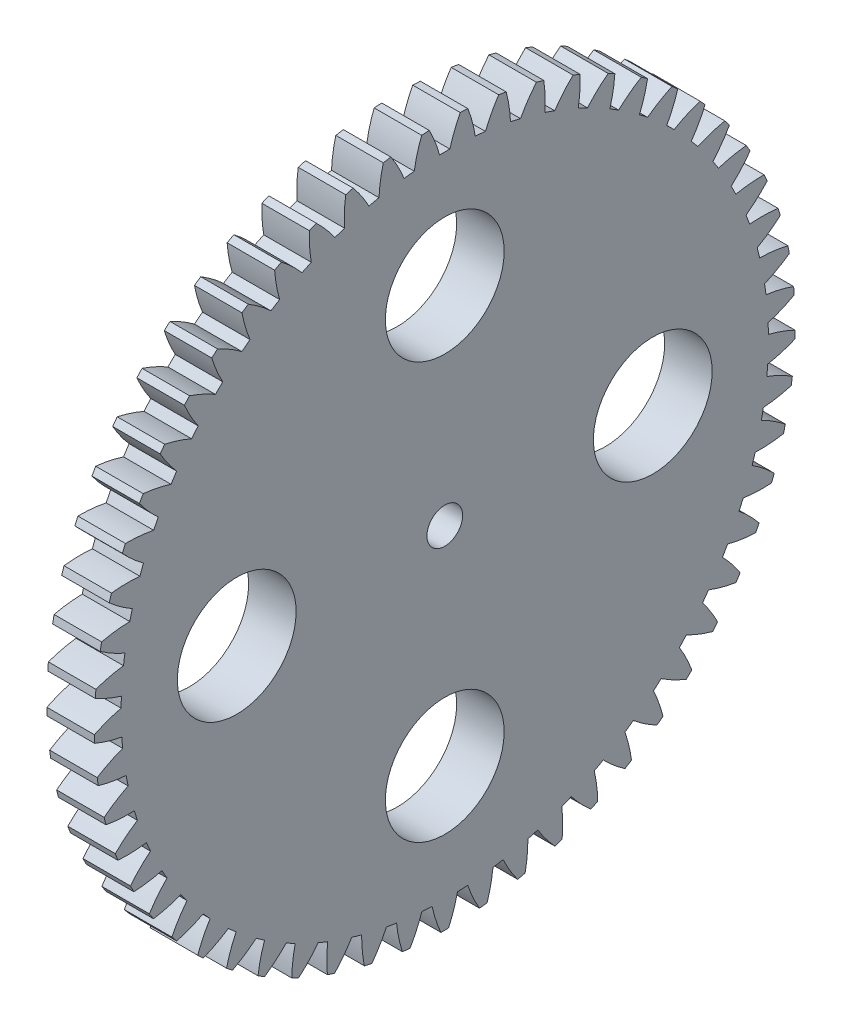
SolidWorks part; units mm, degrees
ref_plane "Plane1" through (0, 0, 0) normal (0, 0, 1) x (1, 0, 0)
ref_plane "Plane2" through (0, 0, 0) normal (0, 1, 0) x (1, 0, 0)
ref_plane "Plane3" through (0, 0, 0) normal (1, 0, 0) x (0, 0, -1)
sketch "HoldingSke" plane through (0, 0, 0) normal (0, 1, 0) x (1, 0, 0)
  line L0 (0, 0) -> (0.5446, -0.8387)
  line L1 (-15, 0) -> (100, 0) construction
  line L2 (0, 0) -> (-2.1039, 2.3779)
  line L3 (0, 0) -> (-11.863, 4.5341)
  line L4 (0, 0) -> (4.7035, 7.2428)
  line L5 (0, 0) -> (-46.8476, -17.4728)
  line L6 (0, 0) -> (-3.3159, -2.2372)
  line L7 (-2.1039, 2.3779) -> (8.6586, 51.2059)
  line L8 (-76.2, 54.61) -> (-75.7, 54.61)
  line L9 (-71.009, 38.7566) -> (-53.1078, 45.2721)
  line L10 (-76.2, 71.12) -> (104.1128, 71.12)
  line L11 (0, 0) -> (-4, 0)
  line L12 (-76.2, 101.6) -> (-76.162, 101.6)
  line L13 (24.9733, 27.94) -> (52.9518, 28.4284)
  line L14 (24.9733, 27.94) -> (24.9743, 27.94)
  line L15 (24.9733, 27.94) -> (100.4006, 29.5858)
  line L16 (-63.627, -1) -> (-12.827, -1)
  circle A0 centre (0, 0) radius 1.5
  circle A1 centre (0, 0) radius 27.249
  circle A2 centre (0, 0) radius 37.5
  circle A3 centre (0, 0) radius 1.5
  dimension "MHD" = 54.498
  dimension "Hub_dia" = 75
  dimension "Bore" = 3
  dimension "MBD" = 3
  dimension "Num_teeth" = 57
  dimension "Pitch" = 1
  dimension "Overall_len" = 50
  dimension "Show_teeth" = 57
  dimension "Thickness" = 4
  dimension "OAL" = 50.0001
  dimension "T_dim" = 0.5
  dimension "Ap" = 20
  dimension "H" = 19.05
  dimension "Pitch_radius" = 180.3128
  dimension "Width" = 4
  dimension "Backlash" = 0.038
  dimension "Addendum_fac" = 1
  dimension "Dedendum_fac" = 1.25
  dimension "Clearance_fac" = 0.25
  dimension "Dedendum_add" = 0.001
  dimension "Module" = 1
sketch "BasProSke" plane through (0, 0, 0) normal (0, 1, 0) x (1, 0, 0)
  line L0 (-10, 0) -> (60, 0) construction
  line L1 (0, 0) -> (0, 29.5)
  line L2 (0, 0) -> (4, 0)
  line L3 (4, 0) -> (4, 29.5)
  line L4 (4, 29.5) -> (0, 29.5)
  dimension "Thickness" = 4
  dimension "Diameter" = 59
revolve "Base-Revolve" add sketch "BasProSke" angle 360 about L0
sketch "TooCutSke" plane through (0, 0, 0) normal (1, 0, 0) x (0, 0, -1)
  line L1 (0, 0) -> (0, 107) construction
  line L2 (0, 0) -> (-0.8518, 28.4873) construction
  line L3 (0, 0) -> (-3.139, 56.8953) construction
  line L4 (-0.8518, 28.4873) -> (-1.5695, 28.4477) construction
  arc A0 (0.4321, 27.2456) -> (-0.4321, 27.2456) centre (0, 0) ccw
  arc A1 (1.3171, 29.496) -> (-1.3171, 29.496) centre (0, 0) ccw
  circle A2 centre (0, 0) radius 28.5 construction
  circle A3 centre (0, 0) radius 26.7812 construction
  arc A4 (-0.4321, 27.2456) -> (-1.3171, 29.496) centre (-11.424, 24.2225) ccw
  arc A5 (1.3171, 29.496) -> (0.4321, 27.2456) centre (11.424, 24.2225) ccw
  dimension "Root_dia" = 54.498
  dimension "Overcut_dia" = 59.0508
  dimension "Pitch_dia" = 57
  dimension "Base_dia" = 53.5625
  dimension "Flank_rad" = 11.4
  dimension "Half_ang" = 3.158
  dimension "Half_CT" = 0.7188
extrude "ToothCut" cut sketch "TooCutSke" along normal through all
fillet "Breaks" [suppressed] radius 0.02
fillet "RootFillets" [suppressed] radius 0.251
pattern_circular "TeethCuts" count 57 every 6.316 about axis through (-10, 0, 0) along (1, 0, 0) of "ToothCut", "RootFillets", "Breaks"
sketch "HubNeaOneSke" plane through (0, 0, 0) normal (-1, 0, 0) x (0, 0, 1)
  circle A0 centre (0, 0) radius 27.249
  dimension "Diameter" = 54.498
extrude "HubNearOne" [suppressed] add sketch "HubNeaOneSke" along normal blind 46.0001
sketch "HubNeaBotSke" plane through (0, 0, 0) normal (-1, 0, 0) x (0, 0, 1)
  circle A0 centre (0, 0) radius 27.249
  dimension "Diameter" = 54.498
extrude "HubNearBoth" [suppressed] add sketch "HubNeaBotSke" along normal blind 23
ref_plane "FarPln" through (4, 0, 0) normal (1, 0, 0) x (0, 0, -1)
sketch "HubFarSke" plane through (4, 0, 0) normal (1, 0, 0) x (0, 0, -1)
  circle A0 centre (0, 0) radius 27.249
  dimension "Diameter" = 54.498
extrude "HubFar" [suppressed] add sketch "HubFarSke" along normal blind 23
sketch "BorSke" plane through (0, 0, 0) normal (1, 0, 0) x (0, 0, -1)
  circle A0 centre (0, 0) radius 1.5
  dimension "Diameter" = 3
extrude "Bore" cut sketch "BorSke" along normal mid plane 100.0001
sketch "KeySke" plane through (0, 0, 0) normal (1, 0, 0) x (0, 0, -1)
  line L0 (-0.6, 0) -> (-0.6, 2)
  line L1 (-0.6, 2) -> (0.6, 2)
  line L2 (0.6, 2) -> (0.6, 0)
  line L3 (0, 0) -> (0, 34) construction
  line L4 (-0.6, 0) -> (0.6, 0)
  dimension "Offset" = 2
  dimension "Width" = 1.2
extrude "Keyway" [suppressed] cut sketch "KeySke" along normal mid plane 100.0001
pattern_circular "Keyway2" [suppressed] count 2 every 90 about axis through (-10, 0, 0) along (1, 0, 0)
sketch "Sketch1" plane through (4, 0, 0) normal (1, 0, 0) x (0, 0, -1)
  circle A0 centre (0, -17.5134) radius 5
  circle A1 centre (-17.5134, 0) radius 5
  circle A2 centre (0, 17.5134) radius 5
  circle A3 centre (17.5134, 0) radius 5
  point P11 (0, 0)
  dimension "D2" = 10
  dimension "D1" = 4
extrude "Cut-Extrude1" cut sketch "Sketch1" against normal blind 10
equation "' \"Module@HoldingSke\" = 6.35"
equation "' \"Num_teeth@HoldingSke\" = 12"
equation "' \"Ap@HoldingSke\" =  20"
equation "' \"Ap@HoldingSke\" = 20"
equation "' \"Width@HoldingSke\" = 0.5 * 25.4"
equation "' \"Hub_dia@HoldingSke\"= 1 * 25.4"
equation "' \"Hub_dia@HoldingSke\" = 1 * 25.4"
equation "' \"Overall_len@HoldingSke\" = 1.0 * 25.4"
equation "' \"Bore@HoldingSke\" = 0.75 * 25.4"
equation "' \"T_dim@HoldingSke\" = 0.1 * 25.4"
equation "' \"Width@KeySke\" = 0.25 * 25.4"
equation "' \"Show_teeth@HoldingSke\" = 13"
equation "' \"Backlash@HoldingSke\" = 0.009 * 25.4"
equation "' \"Addendum_fac@HoldingSke\" = 1.0"
equation "' \"Dedendum_fac@HoldingSke\" = 1.25"
equation "' \"Dedendum_add@HoldingSke\" = 0.00005 * 25.4"
equation "' \"Clearance_fac@HoldingSke\" = 0.25"
equation "\"Pitch@HoldingSke\" = 1 / \"Module@HoldingSke\""
equation "\"Overcut_dia@TooCutSke\" = (\"Num_teeth@HoldingSke\" + 2 * \"Addendum_fac@HoldingSke\") / \"Pitch@HoldingSke\" + 0.002 * 25.4"
equation "\"Pitch_dia@TooCutSke\" = \"Num_teeth@HoldingSke\" / \"Pitch@HoldingSke\""
equation "\"Base_dia@TooCutSke\" = \"Num_teeth@HoldingSke\" / \"Pitch@HoldingSke\" * cos((\"Ap@HoldingSke\"  * 3.14159265 / 180))"
equation "\"Root_dia@TooCutSke\" = (\"Num_teeth@HoldingSke\" + 2) / \"Pitch@HoldingSke\" - 2 * (\"Addendum_fac@HoldingSke\" + \"Dedendum_fac@HoldingSke\") / \"Pitch@HoldingSke\" - \"Dedendum_add@HoldingSke\" * 2"
equation "\"Half_ang@TooCutSke\" = 180 / \"Num_teeth@HoldingSke\""
equation "\"Half_CT@TooCutSke\" = \"Num_teeth@HoldingSke\" / \"Pitch@HoldingSke\" * sin((3.14159265 / 2 / \"Num_teeth@HoldingSke\")) / 2 - 7 * \"Backlash@HoldingSke\" / 4"
equation "\"Flank_rad@TooCutSke\" = \"Num_teeth@HoldingSke\" / \"Pitch@HoldingSke\" / 5"
equation "\"Radius@RootFillets\" = \"Clearance_fac@HoldingSke\" / \"Pitch@HoldingSke\" + \"Dedendum_add@HoldingSke\""
equation "\"Break_rad@Breaks\" = 0.02 / \"Pitch@HoldingSke\""
equation "\"Thickness@HoldingSke\" = \"Width@HoldingSke\""
equation "\"OAL@HoldingSke\" = \"Thickness@HoldingSke\""
equation "\"MHD@HoldingSke\" = (\"Num_teeth@HoldingSke\" + 2) / \"Pitch@HoldingSke\" - 2 * (\"Addendum_fac@HoldingSke\" + \"Dedendum_fac@HoldingSke\")  / \"Pitch@HoldingSke\" - \"Dedendum_add@HoldingSke\" * 2"
equation "\"MBD@HoldingSke\" = (\"Num_teeth@HoldingSke\" + 2) / \"Pitch@HoldingSke\" - 2 * (\"Addendum_fac@HoldingSke\" + \"Dedendum_fac@HoldingSke\")  / \"Pitch@HoldingSke\" - \"Dedendum_add@HoldingSke\" * 2 - 0.002 * 25.4"
equation "\"MHD@HoldingSke\" = ((sgn( \"MHD@HoldingSke\" - \"Hub_dia@HoldingSke\" )-1)*( \"MHD@HoldingSke\" - \"Hub_dia@HoldingSke\" ))/-2+ \"Hub_dia@HoldingSke\""
equation "\"MBD@HoldingSke\" = ((sgn( \"MBD@HoldingSke\" - \"Bore@HoldingSke\" )-1)*( \"MBD@HoldingSke\" - \"Bore@HoldingSke\" ))/-2+ \"Bore@HoldingSke\""
equation "\"OAL@HoldingSke\" = ((sgn( \"OAL@HoldingSke\" - \"Overall_len@HoldingSke\" )+1)*( \"OAL@HoldingSke\" - \"Overall_len@HoldingSke\" ))/2 + \"Overall_len@HoldingSke\" + 0.000002 * 25.4"
equation "\"Num_teeth@TeethCuts\" = int( \"Show_teeth@HoldingSke\" ) + 1"
equation "\"Num_teeth@TeethCuts\" = ((sgn( \"Num_teeth@TeethCuts\" - \"Num_teeth@HoldingSke\" )-1)*( \"Num_teeth@TeethCuts\" - \"Num_teeth@HoldingSke\" ))/-2+ \"Num_teeth@HoldingSke\""
equation "\"Num_teeth@TeethCuts\" = ((sgn( \"Num_teeth@TeethCuts\" - 2.0)+1)*( \"Num_teeth@TeethCuts\" - 2.0))/2 +2.0"
equation "\"Angle@TeethCuts\" = 360.0 / \"Num_teeth@HoldingSke\""
equation "\"Diameter@BasProSke\" = (\"Num_teeth@HoldingSke\" + 2 * \"Addendum_fac@HoldingSke\") / \"Pitch@HoldingSke\""
equation "\"Thickness@BasProSke\"  = \"Thickness@HoldingSke\""
equation "' \"Fillet_rad@BasProSke\" =  \"Thickness@HoldingSke\" * 0.05"
equation "' \"Fillet_rad@BasProSke\" = \"Thickness@HoldingSke\" * 0.05"
equation "\"MHD@HoldingSke\" = ((sgn( \"MHD@HoldingSke\" - \"Root_dia@TooCutSke\" )-1)*( \"MHD@HoldingSke\" - \"Root_dia@TooCutSke\" ))/-2+ \"Root_dia@TooCutSke\""
equation "\"Diameter@HubNeaOneSke\" = \"MHD@HoldingSke\""
equation "\"Length@HubNearOne\" = \"OAL@HoldingSke\" - \"Thickness@BasProSke\""
equation "\"Diameter@HubNeaBotSke\" = \"MHD@HoldingSke\""
equation "\"Length@HubNearBoth\" = ( \"OAL@HoldingSke\" - \"Thickness@BasProSke\" ) / 2.0"
equation "\"Thickness@FarPln\" = \"Thickness@BasProSke\""
equation "\"Diameter@HubFarSke\" = \"MHD@HoldingSke\""
equation "\"Length@HubFar\" = ( \"OAL@HoldingSke\" - \"Thickness@BasProSke\" ) / 2.0"
equation "\"D1@Bore\" = \"OAL@HoldingSke\" * 2.0"
equation "\"D1@Keyway\" = \"OAL@HoldingSke\" * 2.0"
equation "\"Offset@KeySke\" = \"T_dim@HoldingSke\" + \"MBD@HoldingSke\" / 2.0"
